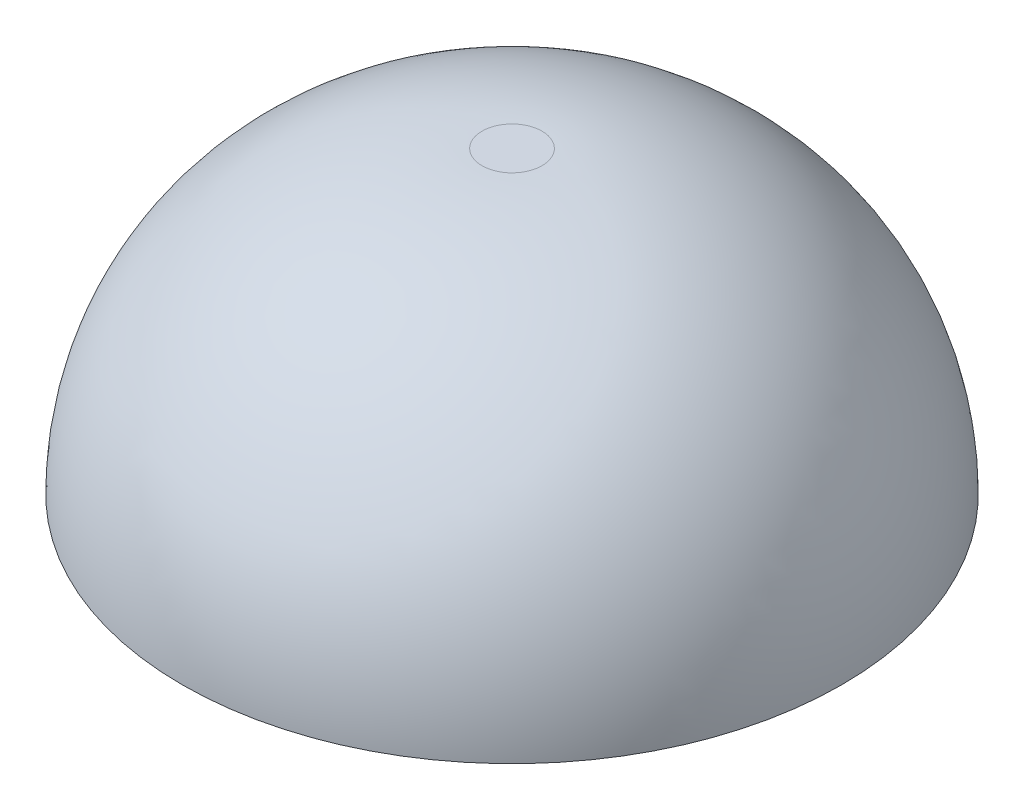
SolidWorks part; units mm, degrees
material "Silicon Rubber"
ref_plane "Front Plane" through (0, 0, 0) normal (0, 0, 1) x (1, 0, 0)
ref_plane "Top Plane" through (0, 0, 0) normal (0, 1, 0) x (1, 0, 0)
ref_plane "Right Plane" through (0, 0, 0) normal (1, 0, 0) x (0, 0, -1)
sketch "Sketch1" plane through (0, 0, 0) normal (1, 0, 0) x (0, 0, -1)
  line L0 (0, 0) -> (0, 7945.2499) construction
  line L1 (0, 0) -> (5.588, 0)
  line L2 (0.508, 5.08) -> (0, 5.08)
  line L3 (0, 5.08) -> (0, 0)
  arc A0 (5.588, 0) -> (0.508, 5.08) centre (0.508, 0) ccw
  dimension "D1" = 5.08
  dimension "D2" = 11.176
revolve "Revolve1" add sketch "Sketch1" angle 360 about L0
